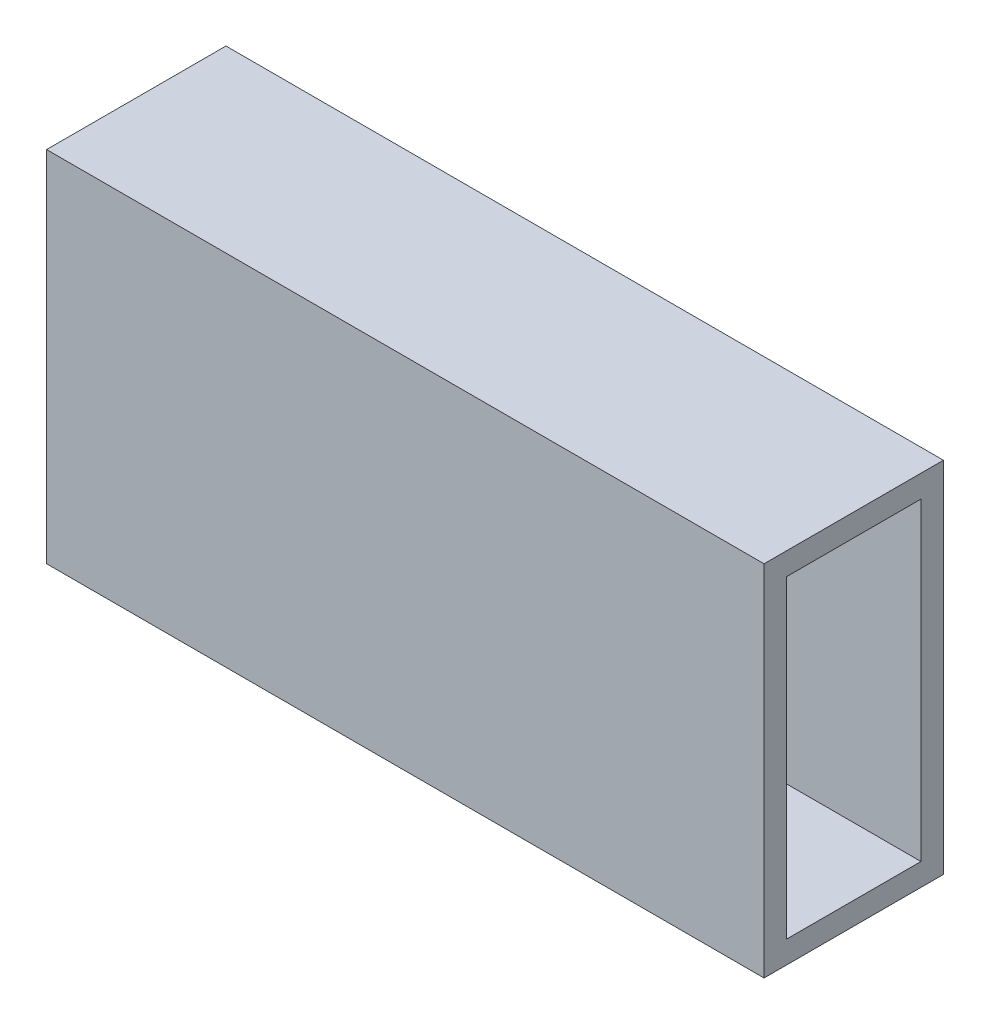
SolidWorks part; units mm, degrees
ref_plane "Front Plane" through (0, 0, 0) normal (0, 0, 1) x (1, 0, 0)
ref_plane "Top Plane" through (0, 0, 0) normal (0, 1, 0) x (1, 0, 0)
ref_plane "Right Plane" through (0, 0, 0) normal (1, 0, 0) x (0, 0, -1)
sketch "Sketch1" plane through (0, 0, 0) normal (1, 0, 0) x (0, 0, -1)
  line L1 (0, 0) -> (25.4, 0)
  line L2 (0, 0) -> (0, 50.8)
  line L3 (0, 50.8) -> (25.4, 50.8)
  line L4 (25.4, 0) -> (25.4, 50.8)
  line L5 (3.175, 47.625) -> (22.225, 47.625)
  line L6 (3.175, 47.625) -> (3.175, 3.175)
  line L7 (3.175, 3.175) -> (22.225, 3.175)
  line L8 (22.225, 47.625) -> (22.225, 3.175)
  dimension "D1" = 3.175
  dimension "D2" = 3.175
  dimension "D3" = 3.175
  dimension "D4" = 3.175
  dimension "D5" = 50.8
  dimension "D6" = 25.4
extrude "Boss-Extrude1" add sketch "Sketch1" along normal blind 254
sketch "Sketch2" plane through (0, 0, -25.4) normal (0, 0, -1) x (-1, 0, 0)
  line L0 (-254, 23.3454) -> (-152.4, 23.3454)
  line L1 (-254, 0) -> (-254, 50.8) construction
  line L3 (-152.4, -17.4734) -> (31.7547, -17.4734)
  line L4 (-152.4, -17.4734) -> (-152.4, 64.1641)
  line L5 (-152.4, 64.1641) -> (31.7547, 64.1641)
  line L6 (31.7547, -17.4734) -> (31.7547, 64.1641)
  line M2 (0, 0) -> (0, 50.8)
  line M3 (0, 50.8) -> (-254, 50.8)
  line M5 (-254, 0) -> (0, 0)
  dimension "D1" = 101.6
extrude "Cut-Extrude1" cut sketch "Sketch2" against normal blind 149.098 contours L4 M5 M2 M3
